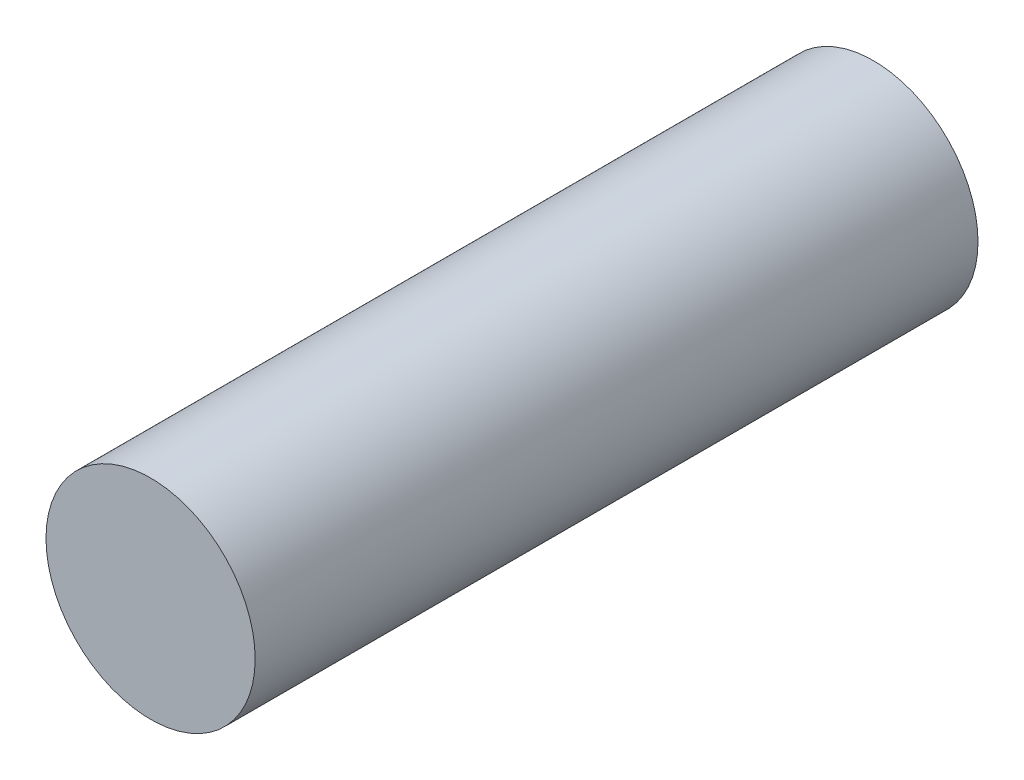
SolidWorks part; units mm, degrees
ref_plane "Front" through (0, 0, 0) normal (0, 0, 1) x (1, 0, 0)
ref_plane "Top" through (0, 0, 0) normal (0, 1, 0) x (1, 0, 0)
ref_plane "Right" through (0, 0, 0) normal (1, 0, 0) x (0, 0, -1)
sketch "Sketch1" plane through (0, 0, 0) normal (0, 0, 1) x (1, 0, 0)
  circle A0 centre (0, 0) radius 7.35
  dimension "D1" = 14.7
extrude "Boss-Extrude1" add sketch "Sketch1" along normal blind 50.8
sketch "Sketch2" plane through (0, 0, 0) normal (0, 0, -1) x (-1, 0, 0)
  circle A0 centre (0, 0) radius 1.985
  dimension "D1" = 3.97
extrude "Cut-Extrude1" cut sketch "Sketch2" against normal blind 6.35
